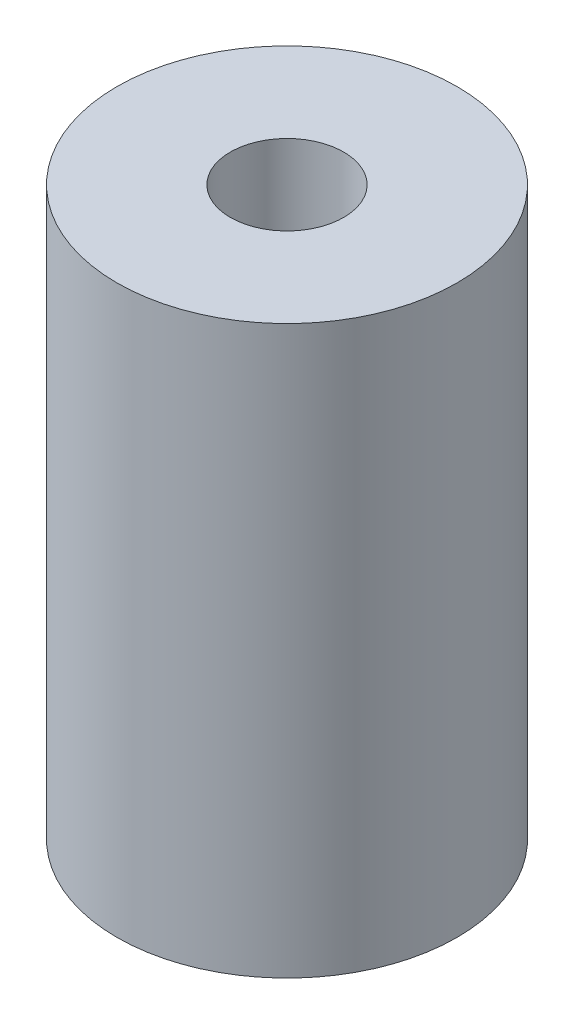
SolidWorks part; units mm, degrees
ref_plane "Front Plane" through (0, 0, 0) normal (0, 0, 1) x (1, 0, 0)
ref_plane "Top Plane" through (0, 0, 0) normal (0, 1, 0) x (1, 0, 0)
ref_plane "Right Plane" through (0, 0, 0) normal (1, 0, 0) x (0, 0, -1)
sketch "Sketch1" plane through (0, 0, 0) normal (0, 1, 0) x (1, 0, 0)
  line L1 (-15, -15) -> (15, -15) construction
  line L2 (-15, -15) -> (-15, 15) construction
  line L3 (-15, 15) -> (15, 15) construction
  line L4 (15, -15) -> (15, 15) construction
  line L5 (-15, -15) -> (15, 15) construction
  line L6 (-15, 15) -> (15, -15) construction
  circle A0 centre (0, 0) radius 15
  point P0 (0, 0)
extrude "Boss-Extrude1" add sketch "Sketch1" along normal blind 50
sketch "Sketch2" plane through (-25, 0, 0) normal (-1, 0, 0) x (0, 0, 1)
  line L0 (-25, 50) -> (25, 0) construction
  line L1 (-25, 0) -> (25, 50) construction
  circle A0 centre (0, 25) radius 5
extrude "Cut-Extrude1" cut sketch "Sketch2" against normal blind 20
sketch "Sketch3" plane through (0, 50, 0) normal (0, 1, 0) x (1, 0, 0)
  line L0 (-25, 25) -> (25, -25) construction
  line L1 (-25, -25) -> (25, 25) construction
  circle A0 centre (0, 0) radius 5
extrude "Cut-Extrude2" cut sketch "Sketch3" against normal blind 10
